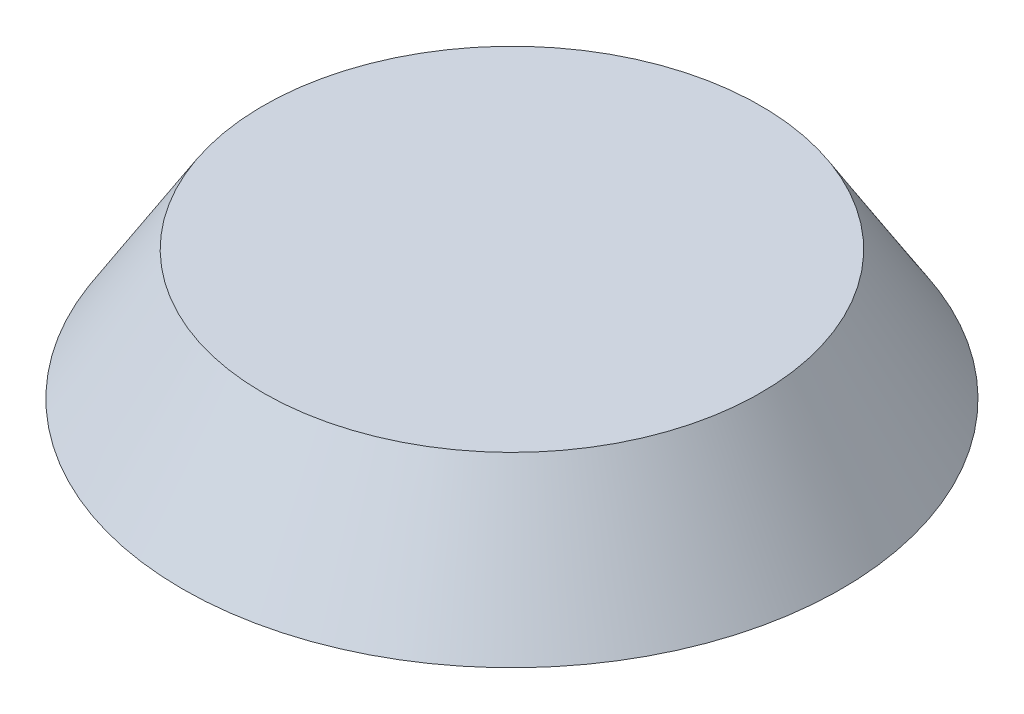
SolidWorks part; units mm, degrees
ref_plane "Ön Düzlem" through (0, 0, 0) normal (0, 0, 1) x (1, 0, 0)
ref_plane "Üst Düzlem" through (0, 0, 0) normal (0, 1, 0) x (1, 0, 0)
ref_plane "Sağ Düzlem" through (0, 0, 0) normal (1, 0, 0) x (0, 0, -1)
sketch "Çizim2" plane through (0, 0, 0) normal (0, 1, 0) x (1, 0, 0)
  circle A0 centre (0, 0) radius 2.44
  circle A1 centre (0, 0) radius 5.096
extrude "Yükseklik-Ekstrüzyon1" add sketch "Çizim2" along normal blind 2 draft 32
sketch "Çizim3" plane through (0, 0, 0) normal (0, 1, 0) x (1, 0, 0)
  circle A0 centre (0, 0) radius 2.44
extrude "Ekstrüzyon-İnce1" add sketch "Çizim3" along normal blind 2 thin
ref_plane "Düzlem1" through (0, 2, 0) normal (0, 1, 0) x (1, 0, 0)
sketch "Çizim4" plane through (0, 2, 0) normal (0, 1, 0) x (1, 0, 0)
  circle A0 centre (0, 0) radius 3.8462
extrude "Yükseklik-Ekstrüzyon2" add sketch "Çizim4" against normal blind 0.2
sketch "Çizim5" plane through (0, 0, 0) normal (0, 1, 0) x (1, 0, 0)
  circle A0 centre (0, 0) radius 1.22
extrude "Ekstrüzyon-İnce2" add sketch "Çizim5" along normal blind 1.8 thin
